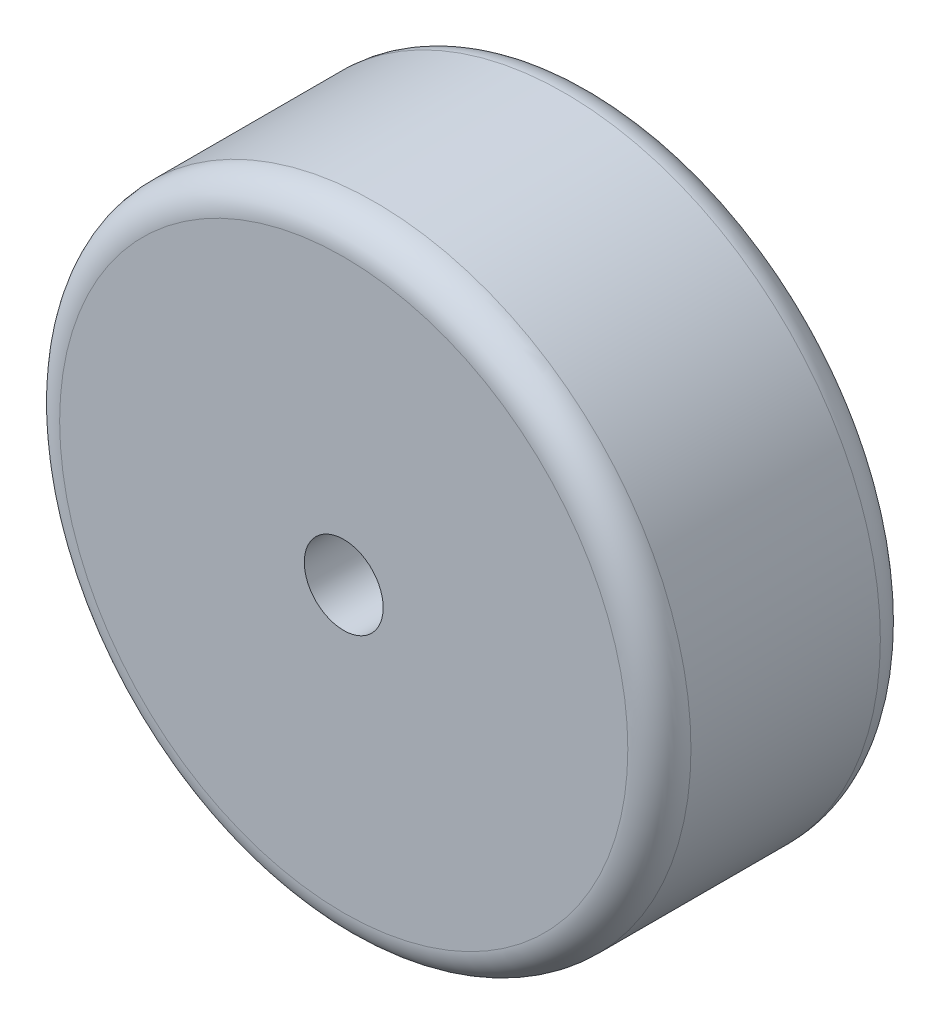
SolidWorks part; units mm, degrees
ref_plane "Front Plane" through (0, 0, 0) normal (0, 0, 1) x (1, 0, 0)
ref_plane "Top Plane" through (0, 0, 0) normal (0, 1, 0) x (1, 0, 0)
ref_plane "Right Plane" through (0, 0, 0) normal (1, 0, 0) x (0, 0, -1)
sketch "Sketch1" plane through (0, 0, 0) normal (0, 0, 1) x (1, 0, 0)
  circle A0 centre (0, 0) radius 25.4
  circle A1 centre (0, 0) radius 3.175
extrude "Boss-Extrude1" add sketch "Sketch1" along normal blind 20.32
fillet "Fillet1" radius 2.54 2 edges at (25.4, 0, 0) (25.4, 0, 20.32)
